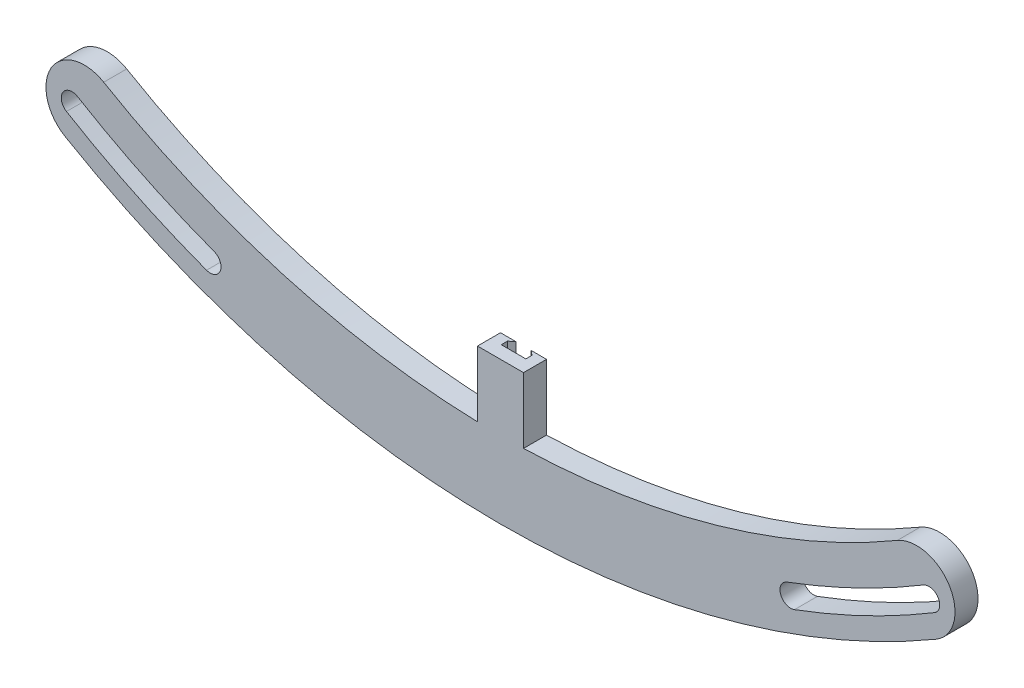
SolidWorks part; units mm, degrees
ref_plane "Front Plane" through (0, 0, 0) normal (0, 0, 1) x (1, 0, 0)
ref_plane "Top Plane" through (0, 0, 0) normal (0, 1, 0) x (1, 0, 0)
ref_plane "Right Plane" through (0, 0, 0) normal (1, 0, 0) x (0, 0, -1)
sketch "Sketch1" plane through (0, 0, 0) normal (1, 0, 0) x (0, 0, -1)
  line L0 (0, 142.748) -> (-3.81, 142.748)
  line L1 (-3.81, 142.748) -> (-3.81, 130.048)
  line L2 (-3.81, 130.048) -> (0, 130.048)
  line L3 (0, 130.048) -> (0, 142.748)
  line L6 (0, 0) -> (62.4328, 0) construction
  dimension "D1" = 142.748
  dimension "D2" = 3.81
  dimension "D3" = 12.7
revolve "Revolve1" add sketch "Sketch1" angle 360 about L6
sketch "Sketch2" plane through (0, 0, 3.81) normal (0, 0, 1) x (1, 0, 0)
  circle A0 centre (0, 137.668) radius 1.778
  circle A1 centre (0, 0) radius 142.748 construction
  circle A2 centre (107.6332, 85.8346) radius 1.778
  circle A3 centre (134.2164, -30.634) radius 1.778
  circle A4 centre (59.7319, -124.0346) radius 1.778
  circle A5 centre (-59.7319, -124.0346) radius 1.778
  circle A6 centre (-134.2164, -30.634) radius 1.778
  circle A7 centre (-107.6332, 85.8346) radius 1.778
  dimension "D1" = 3.556
  dimension "D2" = 137.668
  dimension "D3" = 7
extrude "Cut-Extrude1" cut sketch "Sketch2" against normal mid plane 30.48
sketch "Sketch3" plane through (0, 0, 3.81) normal (0, 0, 1) x (1, 0, 0)
  line L0 (0, 0) -> (-74.2071, -114.269) construction
  line L1 (0, 0) -> (74.2071, -114.269) construction
  line L2 (0, -2.0955) -> (0, 2.0955) construction
  circle A0 centre (0, 0) radius 130.048 construction
  arc A1 (-48.0349, -129.016) -> (-70.9195, -117.9953) centre (0, 0) cw construction
  arc A2 (-71.8354, -119.5193) -> (-48.6553, -130.6823) centre (0, 0) ccw
  arc A3 (-70.0036, -116.4714) -> (-47.4145, -127.3497) centre (0, 0) ccw
  arc A4 (-70.0036, -116.4714) -> (-71.8354, -119.5193) centre (-70.9195, -117.9953) ccw
  arc A5 (-48.6553, -130.6823) -> (-47.4145, -127.3497) centre (-48.0349, -129.016) ccw
  arc A6 (48.0349, -129.016) -> (70.9195, -117.9953) centre (0, 0) ccw construction
  arc A7 (48.6553, -130.6823) -> (71.8354, -119.5193) centre (0, 0) ccw
  arc A8 (47.4145, -127.3497) -> (70.0036, -116.4714) centre (0, 0) ccw
  arc A9 (47.4145, -127.3497) -> (48.6553, -130.6823) centre (48.0349, -129.016) ccw
  arc A10 (71.8354, -119.5193) -> (70.0036, -116.4714) centre (70.9195, -117.9953) ccw
  arc A11 (-65.6748, -112.2466) -> (65.6748, -112.2466) centre (0, 0) ccw
  arc A12 (-72.0883, -123.2082) -> (72.0883, -123.2082) centre (0, 0) ccw
  arc A14 (-65.6748, -112.2466) -> (-72.0883, -123.2082) centre (-68.8816, -117.7274) ccw
  arc A15 (72.0883, -123.2082) -> (65.6748, -112.2466) centre (68.8816, -117.7274) ccw
  point P9 (-59.7319, -124.0346)
  point P14 (59.7319, -124.0346)
  circle M1 centre (-107.6332, 85.8346) radius 1.778
  circle M2 centre (-134.2164, -30.634) radius 1.778
  circle M3 centre (-59.7319, -124.0346) radius 1.778
  circle M4 centre (59.7319, -124.0346) radius 1.778
  circle M5 centre (134.2164, -30.634) radius 1.778
  circle M6 centre (107.6332, 85.8346) radius 1.778
  circle M7 centre (0, 137.668) radius 1.778
  circle M8 centre (0, 0) radius 130.048
  circle M9 centre (0, 0) radius 142.748
  dimension "D2" = 1.778
  dimension "D4" = 1.778
  dimension "D10" = 6.35
  dimension "D11" = 6.35
  dimension "D1" = 25.4
  dimension "D3" = 25.4
  dimension "D5" = 33
  dimension "D6" = 33
extrude "Cut-Extrude2" cut sketch "Sketch3" against normal through all contours A3 A4 A2 M3 | A2 A5 A3 M3 | A8 A9 A7 M4 | A7 A10 A8 M4 | A15 A14 M9 M8 M2 M6 M7 M5 M1
ref_plane "Plane1" through (0, -130.048, 0) normal (0, -1, 0) x (1, 0, 0)
sketch "Sketch6" plane through (0, -130.048, 0) normal (0, -1, 0) x (1, 0, 0)
  line L0 (-65.6748, 0) -> (65.6748, 0) construction
  line L1 (3.81, 0) -> (-3.81, 0)
  line L2 (3.81, 0) -> (3.81, 3.81)
  line L3 (3.81, 3.81) -> (-3.81, 3.81)
  line L4 (-3.81, 0) -> (-3.81, 3.81)
  line L5 (65.6748, 3.81) -> (-65.6748, 3.81) construction
  dimension "D1" = 3.81
  dimension "D2" = 7.62
extrude "Boss-Extrude1" add sketch "Sketch6" against normal blind 10.922
sketch "Sketch7" plane through (0, -119.126, 0) normal (0, 1, 0) x (1, 0, 0)
  line L0 (-1.27, 0) -> (-2.032, -0.635)
  line L1 (-3.81, 0) -> (3.81, 0) construction
  line L3 (-2.032, -0.635) -> (-2.032, -1.651)
  line L4 (-2.032, -1.651) -> (2.032, -1.651)
  line L7 (2.032, -0.635) -> (1.27, 0)
  line L8 (1.27, 0) -> (-1.27, 0)
  line L9 (2.032, -1.651) -> (2.032, -0.635)
  line L10 (3.81, -3.81) -> (-3.81, -3.81) construction
  point P4 (0, -3.81)
  dimension "D1" = 1.651
  dimension "D2" = 0.762
  dimension "D3" = 1.016
  dimension "D4" = 2.032
  dimension "D5" = 4.064
extrude "Cut-Extrude3" cut sketch "Sketch7" against normal blind 6.096
